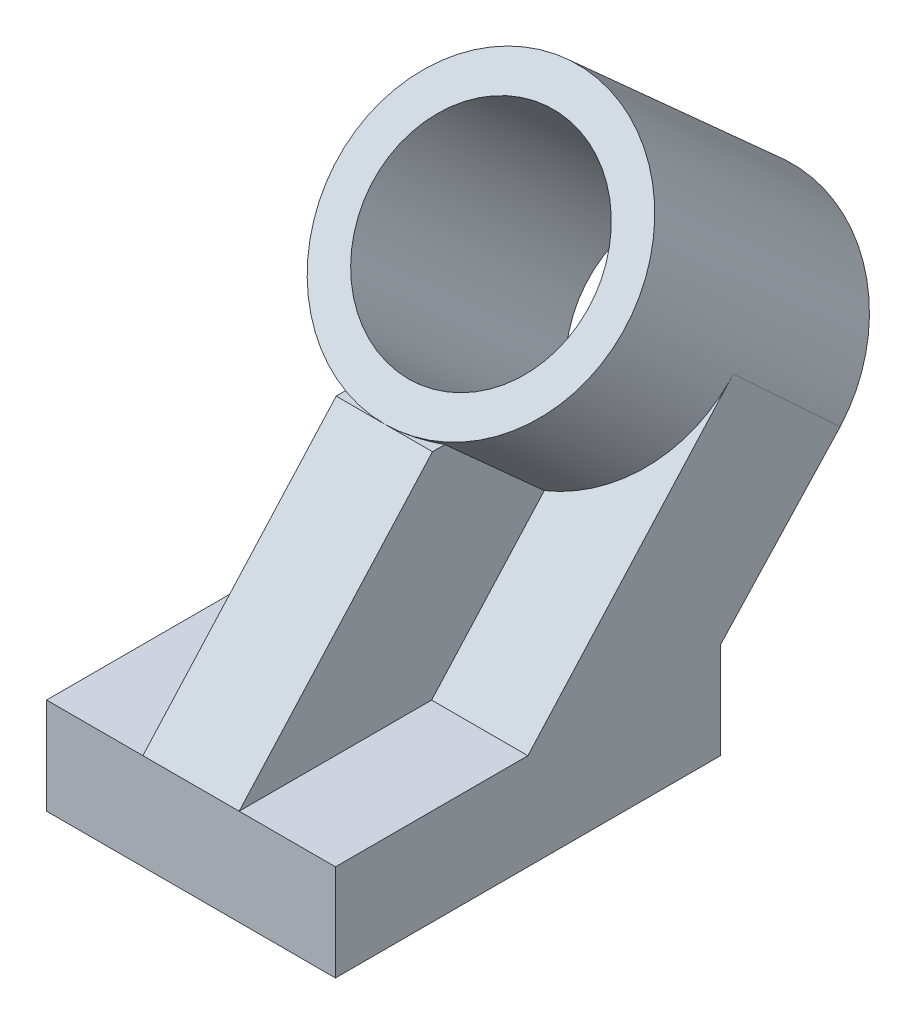
SolidWorks part; units mm, degrees
material "6061 Alloy"
ref_plane "Front Plane" through (0, 0, 0) normal (0, 0, 1) x (1, 0, 0)
ref_plane "Top Plane" through (0, 0, 0) normal (0, 1, 0) x (1, 0, 0)
ref_plane "Right Plane" through (0, 0, 0) normal (1, 0, 0) x (0, 0, -1)
sketch "Sketch5" plane through (0, 0, 0) normal (0, 1, 0) x (1, 0, 0)
  line L0 (38.1, -50.7572) -> (38.1, 50.8428)
  line L1 (38.1, 50.8428) -> (-38.1, 50.8428)
  line L2 (-38.1, 50.8428) -> (-38.1, -50.7572)
  line L3 (-38.1, -50.7572) -> (38.1, -50.7572)
  point P3 (0, 0)
  point P7 (40.3475, -15.7129)
  point P10 (38.1, 0.0428)
  dimension "D1" = 38.1
  dimension "D2" = 76.2
  dimension "D3" = 50.8428
  dimension "D4" = 101.6
  dimension "D5" = 40.3475
  dimension "D6" = 15.7129
extrude "Boss-Extrude2" add sketch "Sketch5" against normal blind 25.4
sketch "Sketch7" plane through (0, 0, 0) normal (1, 0, 0) x (0, 0, -1)
  line L0 (-50.7572, 0) -> (0.2306, 56.6276)
  line L1 (0.2306, 56.6276) -> (50.9878, 56.6276)
  line L3 (0, 0) -> (50.9878, 56.6276)
  line L4 (-50.7572, 0) -> (0, 0)
extrude "Boss-Extrude3" add sketch "Sketch7" along normal mid plane 25.4
sketch "Sketch8" plane through (0, 25.2395, 28.0314) normal (0, 0.6691, 0.7431) x (1, 0, 0)
  line L0 (-12.7, 42.2368) -> (-12.7, -33.9632) construction
  line L1 (12.7, -33.9632) -> (-12.7, -33.9632) construction
  circle A0 centre (0, 80.3368) radius 38.1
extrude "Boss-Extrude4" add sketch "Sketch8" against normal blind 76.2
sketch "Sketch11" plane through (0, 25.2395, 28.0314) normal (0, 0.6691, 0.7431) x (1, 0, 0)
  circle A0 centre (0, 80.3368) radius 28.575
  dimension "D1" = 57.15
sketch "Sketch14" plane through (38.1, 0, 0) normal (1, 0, 0) x (0, 0, -1)
  line L0 (82.3521, 33.9537) -> (50.8428, 0)
  line L1 (56.8582, 5.6399) -> (107.846, 62.2675) construction
  line L2 (50.8428, 0) -> (0, 0)
  line L3 (0, 0) -> (50.664, 56.2681)
  line L4 (50.664, 56.2681) -> (54.2003, 60.0787)
  line L5 (54.2003, 60.0787) -> (82.3521, 33.9537)
extrude "Boss-Extrude7" add sketch "Sketch14" against normal through all
extrude "Cut-Extrude3" cut sketch "Sketch11" against normal through all contours A0
